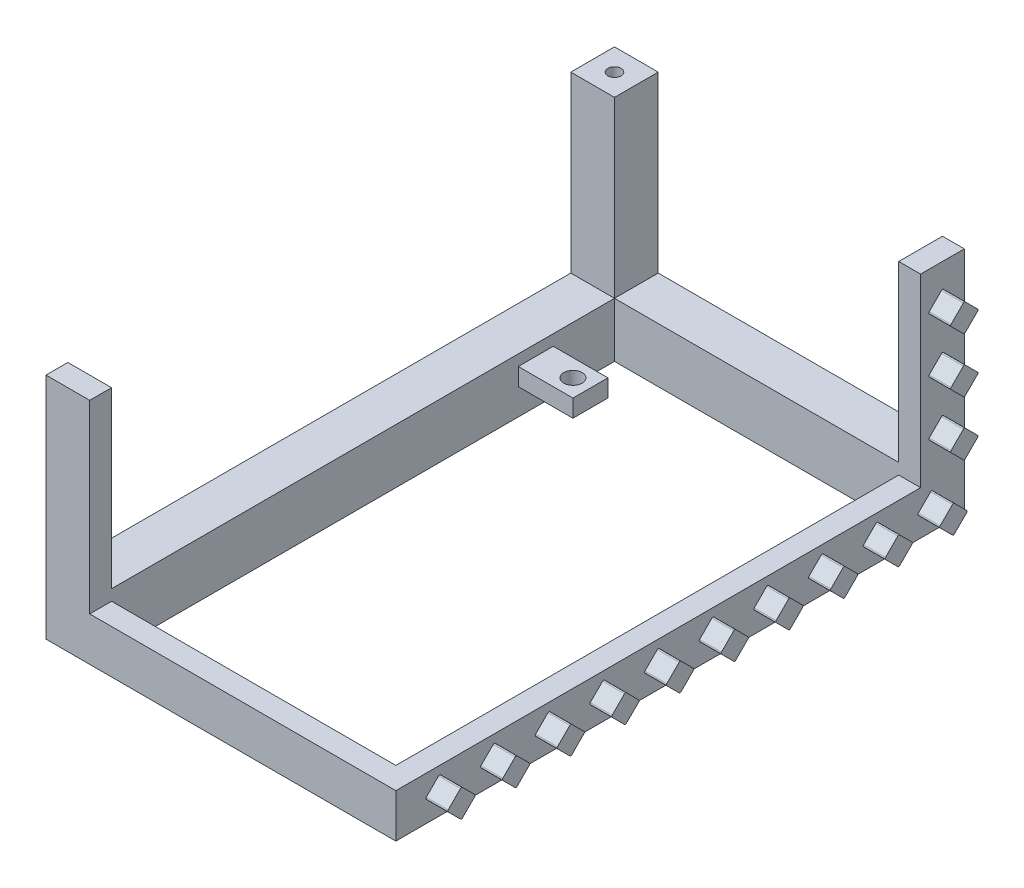
SolidWorks part; units mm, degrees
other "Markup1"
sketch "Sketch26" plane through (40, 52.3, 60) normal (0.2452, 0.2829, 0.9273) x (0.9695, -0.0685, -0.2355)
ref_plane "Front Plane" through (0, 0, 0) normal (0, 0, 1) x (1, 0, 0)
ref_plane "Top Plane" through (0, 0, 0) normal (0, 1, 0) x (1, 0, 0)
ref_plane "Right Plane" through (0, 0, 0) normal (1, 0, 0) x (0, 0, -1)
sketch "Sketch1" plane through (0, 0, 0) normal (0, 1, 0) x (1, 0, 0)
  line L0 (0, 0) -> (0, 70) construction
  line L1 (35, -60) -> (-45, -60)
  line L2 (35, -60) -> (35, 70)
  line L3 (35, 70) -> (-45, 70)
  line L4 (-45, -60) -> (-45, 70)
  line L5 (0, 0) -> (0, -60) construction
  point P0 (0, 0)
  dimension "D1" = 70
  dimension "D2" = 60
extrude "Boss-Extrude1" add sketch "Sketch1" along normal blind 10
sketch "Sketch9" plane through (0, 10, 0) normal (0, 1, 0) x (1, 0, 0)
  line L0 (35, 70) -> (-45, 70)
  line L1 (-45, 70) -> (-45, -60)
  line L2 (-45, -60) -> (-35, -60)
  line L3 (-45, -60) -> (35, -60) construction
  line L4 (35, 70) -> (35, 60)
  line L5 (35, -60) -> (35, 70) construction
  line L6 (35, 60) -> (-35, 60)
  line L7 (-35, -60) -> (-35, 60)
extrude "Boss-Extrude10" add sketch "Sketch9" along normal blind 42.3
sketch "Sketch13" plane through (-35, 0, 0) normal (1, 0, 0) x (0, 0, -1)
  line L5 (60, 52.3) -> (-55, 52.3)
  line L8 (-60, 52.3) -> (60, 52.3) construction
  line L11 (60, 12.5) -> (-55, 12.5)
  line L13 (60, 52.3) -> (60, 12.5)
  line L14 (-55, 52.3) -> (-55, 12.5)
  line L17 (-60, 52.3) -> (-60, 10) construction
  line M9 (-60, 10) -> (60, 10)
  line M12 (60, 10) -> (60, 52.3)
  line M13 (60, 52.3) -> (-60, 52.3)
  dimension "D1" = 5
extrude "Cut-Extrude3" cut sketch "Sketch13" against normal through all contours L14 M13 M9 M12
sketch "Sketch14" plane through (0, 0, -60) normal (0, 0, 1) x (1, 0, 0)
  line L12 (-35, 12.5) -> (30, 12.5)
  line L13 (30, 12.5) -> (30, 52.3)
  line L14 (-45, 52.3) -> (35, 52.3) construction
  line L15 (30, 52.3) -> (-35, 52.3)
  line L16 (-35, 52.3) -> (-35, 12.5)
  line L17 (35, 52.3) -> (35, 10) construction
  dimension "D1" = 5
extrude "Cut-Extrude4" cut sketch "Sketch14" against normal through all
sketch "Sketch15" plane through (0, 52.3, 0) normal (0, 1, 0) x (1, 0, 0)
  line L0 (-40, 70) -> (-40, 65) construction
  line L1 (35, 70) -> (30, 70) construction
  line L2 (-40, 65) -> (-45, 65) construction
  line L3 (-45, 70) -> (-45, 60) construction
  line L4 (30, 60) -> (35, 60) construction
  circle A0 centre (-40, 65) radius 1.5
  dimension "D1" = 5
  dimension "D2" = 5
extrude "Cut-Extrude5" cut sketch "Sketch15" against normal blind 4
sketch "Sketch21" plane through (0, 10, 0) normal (0, 1, 0) x (1, 0, 0)
  line L0 (-26.5, 42) -> (-45, 42) construction
  line L1 (-26.5, 42) -> (-26.5, 70) construction
  line L2 (-35, 70) -> (30, 70) construction
  line L5 (-45, -55) -> (-45, 60) construction
  circle A0 centre (-26.5, 42) radius 2.1
  dimension "D1" = 4.2
extrude "Cut-Extrude8" cut sketch "Sketch21" against normal through all
sketch "Sketch22" plane through (35, 0, 0) normal (1, 0, 0) x (0, 0, -1)
  line L0 (-60, 5) -> (60, 5) construction
  line L1 (-60, 10) -> (-60, 0) construction
  line L2 (70, 52.3) -> (70, 0) construction
  line L3 (60, 10) -> (60, 0) construction
  line L41 (60, 10) -> (70, 10) construction
  line L42 (65, 10) -> (65, 52.3) construction
  line L43 (-60, 0) -> (70, 0) construction
  line L44 (60, 52.3) -> (70, 52.3) construction
  line L56 (68.25, 31.15) -> (61.75, 31.15) construction
  line L73 (0, 8.25) -> (0, 1.75) construction
  line L74 (-0.2121, 8.0379) -> (-3.0379, 5.2121)
  line L75 (-3.0379, 4.7879) -> (-0.2121, 1.9621)
  line L76 (0.2121, 1.9621) -> (3.0379, 4.7879)
  line L77 (3.0379, 5.2121) -> (0.2121, 8.0379)
  line L78 (15.5379, 5.2121) -> (12.7121, 8.0379)
  line L79 (12.2879, 8.0379) -> (9.4621, 5.2121)
  line L80 (9.4621, 4.7879) -> (12.2879, 1.9621)
  line L81 (12.7121, 1.9621) -> (15.5379, 4.7879)
  line L82 (28.0379, 5.2121) -> (25.2121, 8.0379)
  line L83 (24.7879, 8.0379) -> (21.9621, 5.2121)
  line L84 (21.9621, 4.7879) -> (24.7879, 1.9621)
  line L85 (25.2121, 1.9621) -> (28.0379, 4.7879)
  line L86 (40.5379, 5.2121) -> (37.7121, 8.0379)
  line L87 (37.2879, 8.0379) -> (34.4621, 5.2121)
  line L88 (34.4621, 4.7879) -> (37.2879, 1.9621)
  line L89 (37.7121, 1.9621) -> (40.5379, 4.7879)
  line L90 (53.0379, 5.2121) -> (50.2121, 8.0379)
  line L91 (49.7879, 8.0379) -> (46.9621, 5.2121)
  line L92 (46.9621, 4.7879) -> (49.7879, 1.9621)
  line L93 (50.2121, 1.9621) -> (53.0379, 4.7879)
  line L94 (65.5379, 5.2121) -> (62.7121, 8.0379)
  line L95 (62.2879, 8.0379) -> (59.4621, 5.2121)
  line L96 (59.4621, 4.7879) -> (62.2879, 1.9621)
  line L97 (62.7121, 1.9621) -> (65.5379, 4.7879)
  line L98 (-9.4621, 5.2121) -> (-12.2879, 8.0379)
  line L99 (-12.7121, 8.0379) -> (-15.5379, 5.2121)
  line L100 (-15.5379, 4.7879) -> (-12.7121, 1.9621)
  line L101 (-12.2879, 1.9621) -> (-9.4621, 4.7879)
  line L102 (-21.9621, 5.2121) -> (-24.7879, 8.0379)
  line L103 (-25.2121, 8.0379) -> (-28.0379, 5.2121)
  line L104 (-28.0379, 4.7879) -> (-25.2121, 1.9621)
  line L105 (-24.7879, 1.9621) -> (-21.9621, 4.7879)
  line L106 (-34.4621, 5.2121) -> (-37.2879, 8.0379)
  line L107 (-37.7121, 8.0379) -> (-40.5379, 5.2121)
  line L108 (-40.5379, 4.7879) -> (-37.7121, 1.9621)
  line L109 (-37.2879, 1.9621) -> (-34.4621, 4.7879)
  line L110 (-46.9621, 5.2121) -> (-49.7879, 8.0379)
  line L111 (-50.2121, 8.0379) -> (-53.0379, 5.2121)
  line L112 (-53.0379, 4.7879) -> (-50.2121, 1.9621)
  line L113 (-49.7879, 1.9621) -> (-46.9621, 4.7879)
  line L114 (61.9621, 31.3621) -> (64.7879, 34.1879)
  line L115 (65.2121, 34.1879) -> (68.0379, 31.3621)
  line L116 (68.0379, 30.9379) -> (65.2121, 28.1121)
  line L117 (64.7879, 28.1121) -> (61.9621, 30.9379)
  line L118 (64.7879, 40.6121) -> (61.9621, 43.4379)
  line L119 (61.9621, 43.8621) -> (64.7879, 46.6879)
  line L120 (65.2121, 46.6879) -> (68.0379, 43.8621)
  line L121 (68.0379, 43.4379) -> (65.2121, 40.6121)
  line L122 (64.7879, 15.6121) -> (61.9621, 18.4379)
  line L123 (61.9621, 18.8621) -> (64.7879, 21.6879)
  line L124 (65.2121, 21.6879) -> (68.0379, 18.8621)
  line L125 (68.0379, 18.4379) -> (65.2121, 15.6121)
  arc A56 (-3.0379, 5.2121) -> (-3.0379, 4.7879) centre (-2.8257, 5) ccw
  arc A57 (0.2121, 1.9621) -> (-0.2121, 1.9621) centre (0, 2.1743) cw
  arc A58 (3.0379, 4.7879) -> (3.0379, 5.2121) centre (2.8257, 5) ccw
  arc A59 (0.2121, 8.0379) -> (-0.2121, 8.0379) centre (0, 7.8257) ccw
  arc A60 (12.7121, 8.0379) -> (12.2879, 8.0379) centre (12.5, 7.8257) ccw
  arc A61 (15.5379, 4.7879) -> (15.5379, 5.2121) centre (15.3257, 5) ccw
  arc A62 (9.4621, 5.2121) -> (9.4621, 4.7879) centre (9.6743, 5) ccw
  arc A63 (12.7121, 1.9621) -> (12.2879, 1.9621) centre (12.5, 2.1743) cw
  arc A64 (25.2121, 8.0379) -> (24.7879, 8.0379) centre (25, 7.8257) ccw
  arc A65 (28.0379, 4.7879) -> (28.0379, 5.2121) centre (27.8257, 5) ccw
  arc A66 (21.9621, 5.2121) -> (21.9621, 4.7879) centre (22.1743, 5) ccw
  arc A67 (25.2121, 1.9621) -> (24.7879, 1.9621) centre (25, 2.1743) cw
  arc A68 (37.7121, 8.0379) -> (37.2879, 8.0379) centre (37.5, 7.8257) ccw
  arc A69 (40.5379, 4.7879) -> (40.5379, 5.2121) centre (40.3257, 5) ccw
  arc A70 (34.4621, 5.2121) -> (34.4621, 4.7879) centre (34.6743, 5) ccw
  arc A71 (37.7121, 1.9621) -> (37.2879, 1.9621) centre (37.5, 2.1743) cw
  arc A72 (50.2121, 8.0379) -> (49.7879, 8.0379) centre (50, 7.8257) ccw
  arc A73 (53.0379, 4.7879) -> (53.0379, 5.2121) centre (52.8257, 5) ccw
  arc A74 (46.9621, 5.2121) -> (46.9621, 4.7879) centre (47.1743, 5) ccw
  arc A75 (50.2121, 1.9621) -> (49.7879, 1.9621) centre (50, 2.1743) cw
  arc A76 (62.7121, 8.0379) -> (62.2879, 8.0379) centre (62.5, 7.8257) ccw
  arc A77 (65.5379, 4.7879) -> (65.5379, 5.2121) centre (65.3257, 5) ccw
  arc A78 (59.4621, 5.2121) -> (59.4621, 4.7879) centre (59.6743, 5) ccw
  arc A79 (62.7121, 1.9621) -> (62.2879, 1.9621) centre (62.5, 2.1743) cw
  arc A80 (-12.2879, 8.0379) -> (-12.7121, 8.0379) centre (-12.5, 7.8257) ccw
  arc A81 (-9.4621, 4.7879) -> (-9.4621, 5.2121) centre (-9.6743, 5) ccw
  arc A82 (-15.5379, 5.2121) -> (-15.5379, 4.7879) centre (-15.3257, 5) ccw
  arc A83 (-12.2879, 1.9621) -> (-12.7121, 1.9621) centre (-12.5, 2.1743) cw
  arc A84 (-24.7879, 8.0379) -> (-25.2121, 8.0379) centre (-25, 7.8257) ccw
  arc A85 (-21.9621, 4.7879) -> (-21.9621, 5.2121) centre (-22.1743, 5) ccw
  arc A86 (-28.0379, 5.2121) -> (-28.0379, 4.7879) centre (-27.8257, 5) ccw
  arc A87 (-24.7879, 1.9621) -> (-25.2121, 1.9621) centre (-25, 2.1743) cw
  arc A88 (-37.2879, 8.0379) -> (-37.7121, 8.0379) centre (-37.5, 7.8257) ccw
  arc A89 (-34.4621, 4.7879) -> (-34.4621, 5.2121) centre (-34.6743, 5) ccw
  arc A90 (-40.5379, 5.2121) -> (-40.5379, 4.7879) centre (-40.3257, 5) ccw
  arc A91 (-37.2879, 1.9621) -> (-37.7121, 1.9621) centre (-37.5, 2.1743) cw
  arc A92 (-49.7879, 8.0379) -> (-50.2121, 8.0379) centre (-50, 7.8257) ccw
  arc A93 (-46.9621, 4.7879) -> (-46.9621, 5.2121) centre (-47.1743, 5) ccw
  arc A94 (-53.0379, 5.2121) -> (-53.0379, 4.7879) centre (-52.8257, 5) ccw
  arc A95 (-49.7879, 1.9621) -> (-50.2121, 1.9621) centre (-50, 2.1743) cw
  arc A96 (61.9621, 30.9379) -> (61.9621, 31.3621) centre (62.1743, 31.15) cw
  arc A97 (65.2121, 28.1121) -> (64.7879, 28.1121) centre (65, 28.3243) cw
  arc A98 (68.0379, 30.9379) -> (68.0379, 31.3621) centre (67.8257, 31.15) ccw
  arc A99 (64.7879, 34.1879) -> (65.2121, 34.1879) centre (65, 33.9757) cw
  arc A100 (65.2121, 40.6121) -> (64.7879, 40.6121) centre (65, 40.8243) cw
  arc A101 (61.9621, 43.4379) -> (61.9621, 43.8621) centre (62.1743, 43.65) cw
  arc A102 (64.7879, 46.6879) -> (65.2121, 46.6879) centre (65, 46.4757) cw
  arc A103 (68.0379, 43.4379) -> (68.0379, 43.8621) centre (67.8257, 43.65) ccw
  arc A104 (65.2121, 15.6121) -> (64.7879, 15.6121) centre (65, 15.8243) cw
  arc A105 (61.9621, 18.4379) -> (61.9621, 18.8621) centre (62.1743, 18.65) cw
  arc A106 (64.7879, 21.6879) -> (65.2121, 21.6879) centre (65, 21.4757) cw
  arc A107 (68.0379, 18.4379) -> (68.0379, 18.8621) centre (67.8257, 18.65) ccw
  point P12 (0, 5)
  point P16 (-3.25, 5)
  point P22 (3.25, 5)
  point P132 (65, 31.15)
  point P135 (65, 27.9)
  point P141 (65, 34.4)
  dimension "D1" = 0.3
  dimension "D4" = 0.3
  dimension "D2" = 6
  dimension "D3" = 5
  dimension "D5" = 2
  dimension "D6" = 2
extrude "Boss-Extrude11" add sketch "Sketch22" along normal blind 5
sketch "Sketch23" plane through (0, 10, 0) normal (0, 1, 0) x (1, 0, 0)
  line L2 (30, -55) -> (-35, -55)
  line L3 (-35, -60) -> (-35, 60) construction
  line L5 (-35, 60) -> (30, 60)
  line L7 (-22.5, 38) -> (-22.5, 46)
  line L10 (-35, 60) -> (-35, 46)
  line L11 (-35, 46) -> (-22.5, 46)
  line L12 (-22.5, 38) -> (-35, 38)
  line L13 (-35, 38) -> (-35, -55)
  line L14 (30, 60) -> (30, -55)
  circle A0 centre (-26.5, 42) radius 2.1 construction
  dimension "D1" = 4
  dimension "D2" = 4
  dimension "D3" = 4
extrude "Cut-Extrude9" cut sketch "Sketch23" against normal through all
sketch "Sketch24" plane through (0, 0, 0) normal (0, -1, 0) x (1, 0, 0)
  circle A0 centre (-40, -65) radius 1.5 construction
  circle A1 centre (-40, -65) radius 1.5
extrude "Cut-Extrude10" cut sketch "Sketch24" against normal blind 4
sketch "Sketch25" plane through (0, 0, 0) normal (0, -1, 0) x (1, 0, 0)
  line L0 (-22.5, -38) -> (-22.5, -46)
  line L1 (-22.5, -46) -> (-35, -46)
  line L2 (-35, -46) -> (-35, -38)
  line L3 (-35, -38) -> (-22.5, -38)
extrude "Cut-Extrude11" cut sketch "Sketch25" against normal blind 6
